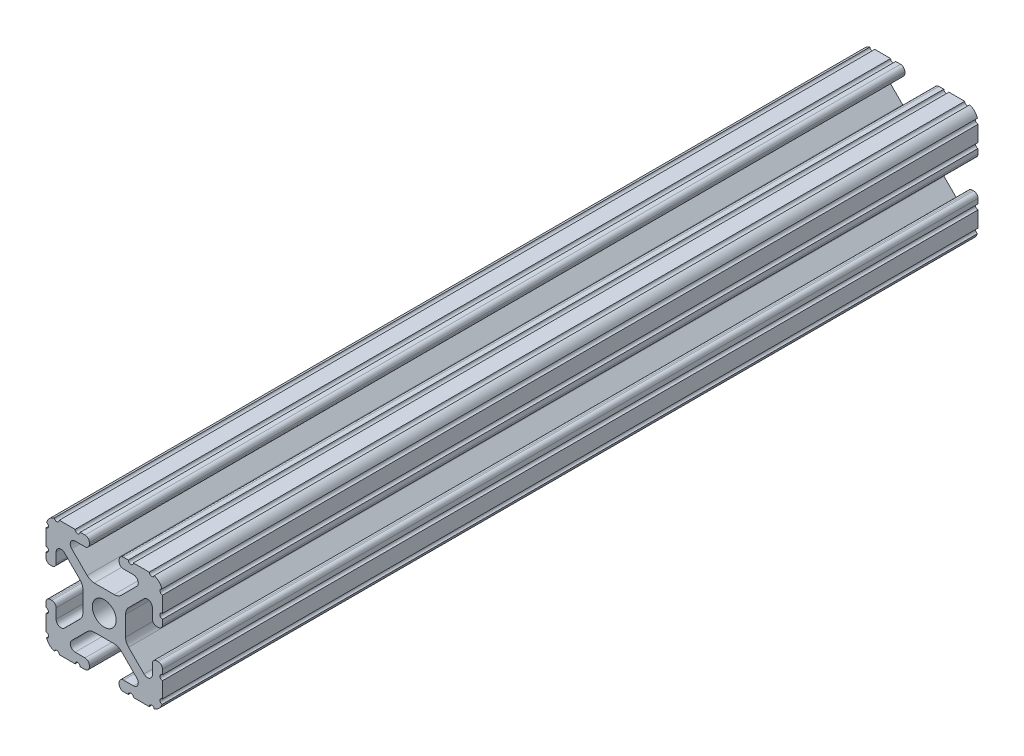
SolidWorks part; units mm, degrees
ref_plane "Front Plane" through (0, 0, 0) normal (0, 0, 1) x (1, 0, 0)
ref_plane "Top Plane" through (0, 0, 0) normal (0, 1, 0) x (1, 0, 0)
ref_plane "Right Plane" through (0, 0, 0) normal (1, 0, 0) x (0, 0, -1)
sketch "Sketch2" plane through (0, 0, 0) normal (0, 0, 1) x (1, 0, 0)
  line L0 (0, 12.7) -> (0, -12.7) construction
  line L1 (-12.7, 0) -> (12.7, 0) construction
  line L2 (3.2512, -12.7) -> (12.7, -12.7)
  line L3 (12.7, -12.7) -> (12.7, -3.2512)
  line L4 (3.2512, -12.7) -> (3.2512, -10.4902)
  line L5 (3.2512, -10.4902) -> (8.9276, -10.4902)
  line L6 (8.9276, -10.4902) -> (3.0856, -4.6482)
  line L7 (0, 0) -> (12.7, -12.7) construction
  line L8 (12.7, -3.2512) -> (10.4902, -3.2512)
  line L9 (10.4902, -3.2512) -> (10.4902, -8.9276)
  line L10 (10.4902, -8.9276) -> (4.6482, -3.0856)
  circle A0 centre (0, 0) radius 2.6035
  arc A1 (6.3485, -10.4902) -> (7.1039, -8.6665) centre (6.3485, -9.4219) ccw construction
  point P8 (0, -4.6482)
  dimension "Center Hole Diameter" = 5.207
  dimension "Rail Height" = 25.4
  dimension "Rail Width" = 25.4
  dimension "T-Slot Width" = 6.5024
  dimension "Slot Inner Width" = 14.8336
  dimension "Thickness" = 2.2098
  dimension "Slot Depth" = 5.842
  dimension "D1" = 2.2098
sketch "Sketch3" plane through (0, 0, 0) normal (1, 0, 0) x (0, 0, -1)
  line L0 (-88.9, -12.7) -> (88.9, -12.7) construction
  line L1 (-80.01, 0) -> (80.01, 0) construction
  dimension "Length" = 177.8
  dimension "D1" = 160.02
sketch "Sketch4" plane through (0, 0, 0) normal (0, 0, 1) x (1, 0, 0)
  line L0 (4.1904, -12.7) -> (10.1173, -12.7)
  line L1 (3.2512, -12.7) -> (12.7, -12.7) construction
  line L2 (3.2512, -12.7) -> (3.2512, -10.4902) construction
  line L3 (3.2512, -10.4902) -> (8.9276, -10.4902) construction
  line L4 (3.2512, -11.4294) -> (3.2512, -11.7608)
  line L5 (4.1904, -10.4902) -> (6.3485, -10.4902)
  line L6 (0, -4.6482) -> (2.164, -4.6482)
  line L7 (8.9276, -10.4902) -> (3.0856, -4.6482) construction
  line L8 (3.7373, -5.2999) -> (7.1039, -8.6665)
  line L9 (12.7, -12.7) -> (12.7, -3.2512) construction
  line L10 (10.4902, -8.9276) -> (4.6482, -3.0856) construction
  line L11 (10.4902, -3.2512) -> (10.4902, -8.9276) construction
  line L12 (10.4902, -6.3485) -> (10.4902, -4.1904)
  line L13 (12.7, -3.2512) -> (10.4902, -3.2512) construction
  line L14 (11.4294, -3.2512) -> (11.7608, -3.2512)
  line L15 (12.7, -4.1904) -> (12.7, -10.1173)
  line L16 (8.6665, -7.1039) -> (5.2999, -3.7373)
  line L17 (4.6482, 0) -> (4.6482, -2.164)
  line L18 (-12.7, 0) -> (12.7, 0) construction
  line L19 (0, -4.6482) -> (0, -2.6035)
  line L20 (0, 12.7) -> (0, -12.7) construction
  line L21 (4.6482, 0) -> (2.6035, 0)
  arc A0 (3.2512, -11.7608) -> (4.1904, -12.7) centre (4.1904, -11.7608) ccw
  arc A2 (3.2512, -11.4294) -> (4.1904, -10.4902) centre (4.1904, -11.4294) cw
  arc A3 (6.3485, -10.4902) -> (7.1039, -8.6665) centre (6.3485, -9.4219) ccw
  arc A4 (2.164, -4.6482) -> (3.7373, -5.2999) centre (2.164, -6.8732) cw
  arc A5 (10.1173, -12.7) -> (12.7, -10.1173) centre (10.1173, -10.1173) ccw
  arc A6 (8.6665, -7.1039) -> (10.4902, -6.3485) centre (9.4219, -6.3485) ccw
  arc A7 (10.4902, -4.1904) -> (11.4294, -3.2512) centre (11.4294, -4.1904) cw
  arc A8 (11.7608, -3.2512) -> (12.7, -4.1904) centre (11.7608, -4.1904) cw
  arc A9 (5.2999, -3.7373) -> (4.6482, -2.164) centre (6.8732, -2.164) cw
  circle A10 centre (0, 0) radius 2.6035 construction
  arc A11 (0, -2.6035) -> (2.6035, 0) centre (0, 0) ccw
  dimension "D1" = 2.5827
  dimension "D2" = 2.225
  dimension "D3" = 0.9392
extrude "Boss-Extrude1" add sketch "Sketch4" along normal mid plane 177.8
sketch "Sketch5" plane through (0, 0, 0) normal (0, 0, 1) x (1, 0, 0)
  line L0 (3.2512, -12.7) -> (12.7, -12.7) construction
  line L1 (4.1904, -10.4902) -> (6.3485, -10.4902) construction
  line L3 (0, 0) -> (12.7, -12.7) construction
  line L4 (6.3485, -10.4902) -> (6.3485, -12.7) construction
  line L5 (8.9276, -10.4902) -> (3.0856, -4.6482) construction
  circle A0 centre (10.3562, -12.7) radius 0.5524
  circle A1 centre (5.796, -12.7) radius 0.5524
  circle A2 centre (12.7, -10.3562) radius 0.5524
  circle A3 centre (12.7, -5.796) radius 0.5524
  point P10 (5.2694, -10.4902)
  point P12 (9.4219, -6.3485)
  dimension "D1" = 1.1049
extrude "Cut-Extrude1" cut sketch "Sketch5" against normal through all both and the other way through all
mirror "Mirror1" about plane through (0, 0, 0) normal (1, 0, 0) of bodies 137 134
mirror "Mirror2" about plane through (0, 0, 0) normal (0, 1, 0) of bodies 135
equation "\"D1@Boss-Extrude1\"=\"Length@Sketch3\""
equation "\"D1@Sketch2\"=\"Thickness@Sketch2\""
equation "\"D2@Sketch4\"=\"Slot Inner Width@Sketch2\"*0.15"
equation "\"D1@Sketch4\"=\"D3@Sketch4\"*2.75"
equation "\"D3@Sketch4\"=\"Thickness@Sketch2\"*0.425"
equation "\"D1@Sketch5\"=\"Thickness@Sketch2\"*0.5"
equation "\"D1@Sketch3\"=\"Length@Sketch3\"*0.9"
